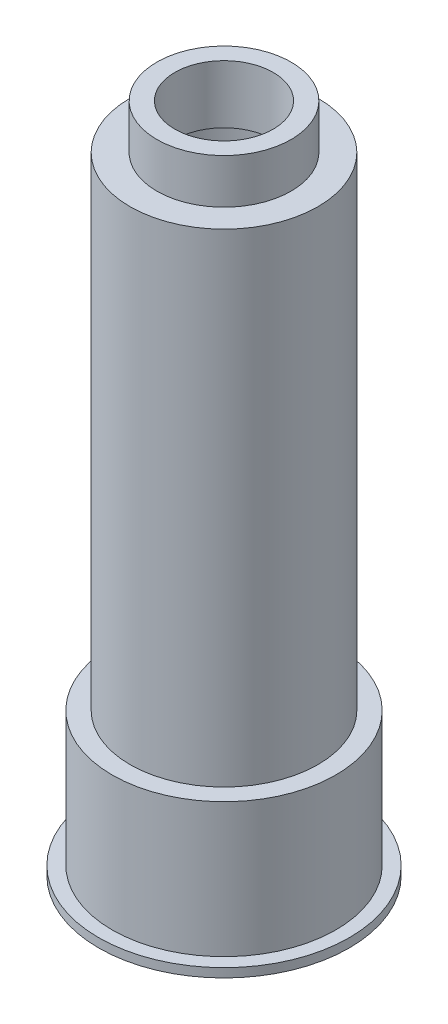
SolidWorks part; units mm, degrees
ref_plane "Frontal" through (0, 0, 0) normal (0, 0, 1) x (1, 0, 0)
ref_plane "Horizontal" through (0, 0, 0) normal (0, 1, 0) x (1, 0, 0)
ref_plane "Profile" through (0, 0, 0) normal (1, 0, 0) x (0, 0, -1)
sketch "Sketch1" plane through (0, 0, 0) normal (0, 1, 0) x (1, 0, 0)
  circle A0 centre (0, 0) radius 14
  circle A1 centre (0, 0) radius 12.5
extrude "Extrude1" add sketch "Sketch1" along normal blind 1
sketch "Sketch2" plane through (0, 1, 0) normal (0, 1, 0) x (-1, 0, 0)
  circle A0 centre (0, 0) radius 12.5
  circle A1 centre (0, 0) radius 10.5
extrude "Extrude2" add sketch "Sketch2" along normal blind 15
ref_plane "Plane1" through (0, 14.5, 0) normal (0, 1, 0) x (-1, 0, 0)
sketch "Sketch4" plane through (0, 14.5, 0) normal (0, 1, 0) x (-1, 0, 0)
  circle A0 centre (0, 0) radius 8.5
  circle A1 centre (0, 0) radius 10.5
extrude "Extrude3" add sketch "Sketch4" along normal blind 55.5
ref_plane "Plane2" through (0, 68.5, 0) normal (0, 1, 0) x (-1, 0, 0)
sketch "Sketch7" plane through (0, 68.5, 0) normal (0, 1, 0) x (-1, 0, 0)
  circle A0 centre (0, 0) radius 5.5
  circle A1 centre (0, 0) radius 8.5
extrude "Extrude6" add sketch "Sketch7" along normal blind 1.5
sketch "Sketch8" plane through (0, 70, 0) normal (0, 1, 0) x (-1, 0, 0)
  circle A0 centre (0, 0) radius 5.5
  circle A1 centre (0, 0) radius 7.5
extrude "Extrude7" add sketch "Sketch8" along normal blind 5
